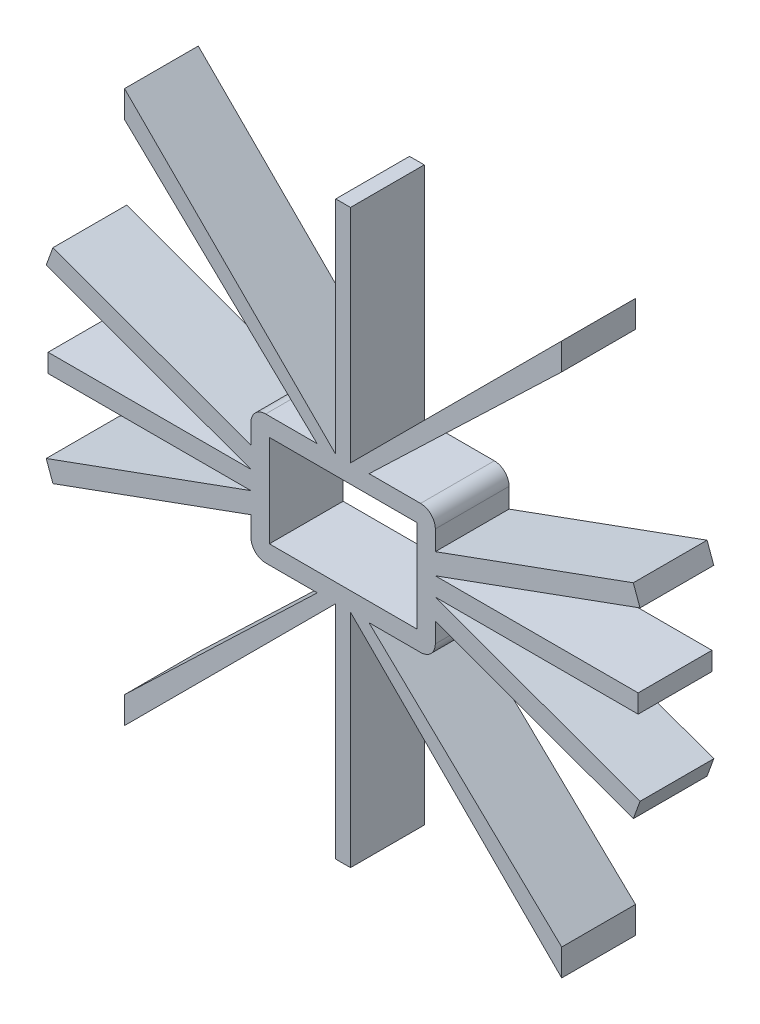
SolidWorks part; units mm, degrees
ref_plane "Front Plane" through (0, 0, 0) normal (0, 0, 1) x (1, 0, 0)
ref_plane "Top Plane" through (0, 0, 0) normal (0, 1, 0) x (1, 0, 0)
ref_plane "Right Plane" through (0, 0, 0) normal (1, 0, 0) x (0, 0, -1)
sketch "Sketch1" plane through (0, 0, 0) normal (0, 0, 1) x (1, 0, 0)
  line L0 (-2.54, 22.225) -> (-2.54, 98.425)
  line L1 (-31.75, 22.225) -> (31.75, 22.225)
  line L2 (-31.75, 22.225) -> (-31.75, -22.225)
  line L3 (-31.75, -22.225) -> (31.75, -22.225)
  line L4 (31.75, 22.225) -> (31.75, -22.225)
  line L5 (-31.75, 22.225) -> (31.75, -22.225) construction
  line L6 (-31.75, -22.225) -> (31.75, 22.225) construction
  line L7 (0, 0) -> (0, 22.225) construction
  line L8 (2.54, 22.225) -> (2.54, 98.425)
  line L9 (-2.54, 98.425) -> (2.54, 98.425)
  line L10 (31.75, 0) -> (101.6, 0) construction
  line L11 (101.6, 3.175) -> (101.6, -3.175)
  line L12 (101.6, -3.175) -> (31.75, -3.175)
  line L13 (2.54, -98.4814) -> (-2.54, -98.4814)
  line L14 (2.54, -22.2814) -> (2.54, -98.4814)
  line L15 (-2.54, -22.2814) -> (-2.54, -98.4814)
  line L16 (101.6, 3.175) -> (31.75, 3.175)
  line L17 (31.75, -3.175) -> (102.2451, -28.8331)
  line L18 (31.75, -10.3662) -> (99.9339, -35.1831)
  line L19 (-2.54, -22.2814) -> (-75.2749, -95.0163)
  line L20 (25.4, 15.875) -> (-25.4, 15.875)
  line L21 (25.4, 15.875) -> (25.4, -15.875)
  line L22 (25.4, -15.875) -> (-25.4, -15.875)
  line L23 (-25.4, 15.875) -> (-25.4, -15.875)
  line L24 (25.4, 15.875) -> (-25.4, -15.875) construction
  line L25 (25.4, -15.875) -> (-25.4, 15.875) construction
  line L26 (-8.8897, -22.225) -> (-75.2749, -85.7814)
  line L27 (-75.2749, -85.7814) -> (-75.2749, -95.0163)
  line L28 (75.2749, -85.7814) -> (75.2749, -95.0163)
  line L29 (2.54, -22.2814) -> (75.2749, -95.0163)
  line L30 (8.8897, -22.225) -> (75.2749, -85.7814)
  line L31 (102.2451, -28.8331) -> (99.9339, -35.1831)
  line L32 (102.2451, 28.8331) -> (99.9339, 35.1831)
  line L33 (31.75, 10.3662) -> (99.9339, 35.1831)
  line L34 (31.75, 3.175) -> (102.2451, 28.8331)
  line L35 (-102.2451, -28.8331) -> (-99.9339, -35.1831)
  line L36 (-101.6, 3.175) -> (-101.6, -3.175)
  line L37 (8.8897, 22.1686) -> (75.2749, 85.725)
  line L38 (2.54, 22.225) -> (75.2749, 94.9599)
  line L39 (75.2749, 85.725) -> (75.2749, 94.9599)
  line L40 (-2.54, 22.225) -> (-75.2749, 94.9599)
  line L41 (-8.8897, 22.1686) -> (-75.2749, 85.725)
  line L42 (-75.2749, 85.725) -> (-75.2749, 94.9599)
  line L43 (-102.2451, 28.8331) -> (-99.9339, 35.1831)
  line L44 (-31.75, 10.3662) -> (-99.9339, 35.1831)
  line L45 (-31.75, 3.175) -> (-102.2451, 28.8331)
  line L46 (-101.6, 3.175) -> (-31.75, 3.175)
  line L47 (-31.75, 0) -> (-101.6, 0) construction
  line L48 (-101.6, -3.175) -> (-31.75, -3.175)
  line L49 (0, 59.0113) -> (0, -67.8938)
  line L50 (98.4532, 2.5118) -> (98.4532, -2.5682) [skipped]
  line L51 (22.2532, 2.5118) -> (98.4532, 2.5118) [skipped]
  line L52 (22.2532, -2.5682) -> (98.4532, -2.5682) [skipped]
  line L53 (22.1968, -8.918) -> (85.7532, -75.3031) [skipped]
  line L54 (22.2532, -2.5682) -> (94.9881, -75.3031) [skipped]
  line L55 (85.7532, -75.3031) -> (94.9881, -75.3031) [skipped]
  line L56 (22.1968, 8.8615) -> (85.7532, 75.2467) [skipped]
  line L57 (85.7532, 75.2467) -> (94.9881, 75.2467) [skipped]
  line L58 (22.2532, 2.5118) -> (94.9881, 75.2467) [skipped]
  line L59 (-22.2532, -2.5682) -> (-98.4532, -2.5682) [skipped]
  line L60 (-22.1968, 8.8615) -> (-85.7532, 75.2467) [skipped]
  line L61 (-22.2532, 2.5118) -> (-94.9881, 75.2467) [skipped]
  line L62 (-85.7532, 75.2467) -> (-94.9881, 75.2467) [skipped]
  line L63 (-22.2532, -2.5682) -> (-94.9881, -75.3031) [skipped]
  line L64 (-22.1968, -8.918) -> (-85.7532, -75.3031) [skipped]
  line L65 (-85.7532, -75.3031) -> (-94.9881, -75.3031) [skipped]
  line L66 (-22.2532, 2.5118) -> (-98.4532, 2.5118) [skipped]
  line L67 (-98.4532, -2.5682) -> (-98.4532, 2.5118) [skipped]
  line L68 (-31.75, -3.175) -> (-102.2451, -28.8331)
  line L69 (-31.75, -10.3662) -> (-99.9339, -35.1831)
  point P0 (0, 0)
  point P15 (0, -98.4814)
  point P27 (0, -0.0282)
  point P63 (0, -0.0282)
  dimension "D1" = 22.225
  dimension "D2" = 31.75
  dimension "D3" = 2.54
  dimension "D5" = 15.875
  dimension "D6" = 25.4
  dimension "D7" = 45
  dimension "D8" = 45
  dimension "D9" = 6.35
  dimension "D10" = 9.2349
  dimension "D12" = 63.5
  dimension "D13" = 69.85
  dimension "D14" = 76.2
  dimension "D15" = 3.175
  dimension "D16" = 70
  dimension "D17" = 70
  dimension "D18" = 6.35
  dimension "D4" = 4
  dimension "D11" = 4
extrude "Boss-Extrude1" add sketch "Sketch1" along normal blind 25.4
fillet "Fillet1" radius 5.08 4 edges at (-31.75, 22.225, 12.7) (-31.75, -22.225, 12.7) (31.75, -22.225, 12.7) (31.75, 22.225, 12.7)
